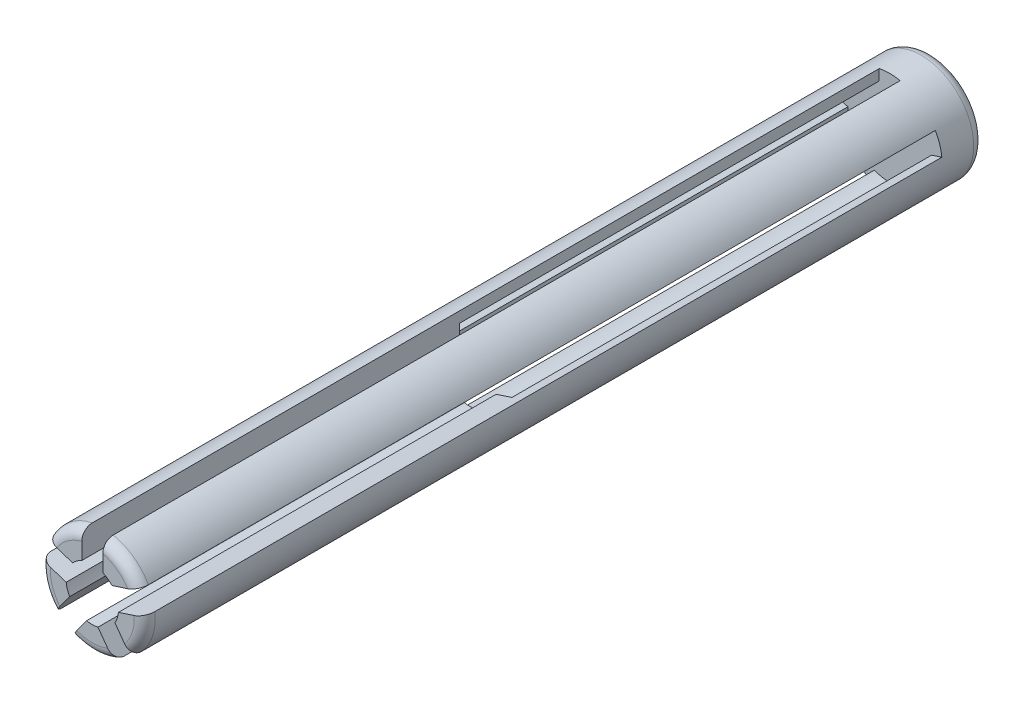
SolidWorks part; units mm, degrees
ref_plane "Front Plane" through (0, 0, 0) normal (0, 0, 1) x (1, 0, 0)
ref_plane "Top Plane" through (0, 0, 0) normal (0, 1, 0) x (1, 0, 0)
ref_plane "Right Plane" through (0, 0, 0) normal (1, 0, 0) x (0, 0, -1)
sketch "Sketch1" plane through (0, 0, 0) normal (0, 0, 1) x (1, 0, 0)
  circle A0 centre (0, 0) radius 6.35
  dimension "D1" = 12.7
extrude "Boss-Extrude1" add sketch "Sketch1" along normal blind 101.6
fillet "Fillet1" radius 1.27 1 edges at (6.35, 0, 0)
sketch "Sketch2" plane through (0, 0, 101.6) normal (0, 0, 1) x (1, 0, 0)
  circle A0 centre (0, 0) radius 3.175
  dimension "D1" = 6.35
extrude "Cut-Extrude1" cut sketch "Sketch2" against normal blind 45.72
sketch "Sketch3" plane through (0, 0, 55.88) normal (0, 0, 1) x (1, 0, 0)
  circle A0 centre (0, 0) radius 5.08
  dimension "D1" = 10.16
extrude "Cut-Extrude2" cut sketch "Sketch3" against normal blind 50.8
fillet "Fillet2" radius 1.27 1 edges at (6.35, 0, 101.6)
sketch "Sketch4" plane through (0, 0, 101.6) normal (0, 0, 1) x (1, 0, 0)
  line L0 (-1.27, 6.2217) -> (-1.27, 2.9099)
  line L1 (1.27, 6.2217) -> (1.27, 2.9099)
  line L2 (-1.27, 2.9099) -> (1.27, 2.9099)
  line L3 (2.3751, 2.1071) -> (3.16, -0.3086)
  line L4 (5.5247, 3.1305) -> (2.3751, 2.1071)
  line L5 (6.3096, 0.7148) -> (3.16, -0.3086)
  line L6 (2.7379, -1.6077) -> (0.683, -3.1007)
  line L7 (4.6845, -4.287) -> (2.7379, -1.6077)
  line L8 (2.6296, -5.78) -> (0.683, -3.1007)
  line L9 (-0.683, -3.1007) -> (-2.7379, -1.6077)
  line L10 (-2.6296, -5.78) -> (-0.683, -3.1007)
  line L11 (-4.6845, -4.287) -> (-2.7379, -1.6077)
  line L12 (-3.16, -0.3086) -> (-2.3751, 2.1071)
  line L13 (-6.3096, 0.7148) -> (-3.16, -0.3086)
  line L14 (-5.5247, 3.1305) -> (-2.3751, 2.1071)
  circle A0 centre (0, 0) radius 3.175 construction
  arc A1 (-1.27, 6.2217) -> (1.27, 6.2217) centre (0, 0) cw
  arc A2 (5.5247, 3.1305) -> (6.3096, 0.7148) centre (0, 0) cw
  arc A3 (4.6845, -4.287) -> (2.6296, -5.78) centre (0, 0) cw
  arc A4 (-2.6296, -5.78) -> (-4.6845, -4.287) centre (0, 0) cw
  arc A5 (-6.3096, 0.7148) -> (-5.5247, 3.1305) centre (0, 0) cw
  point P9 (0, 6.35)
  point P27 (0, 0)
  dimension "D2" = 6.35
  dimension "D1" = 2.54
  dimension "D3" = 5
extrude "Cut-Extrude3" cut sketch "Sketch4" against normal blind 96.52
